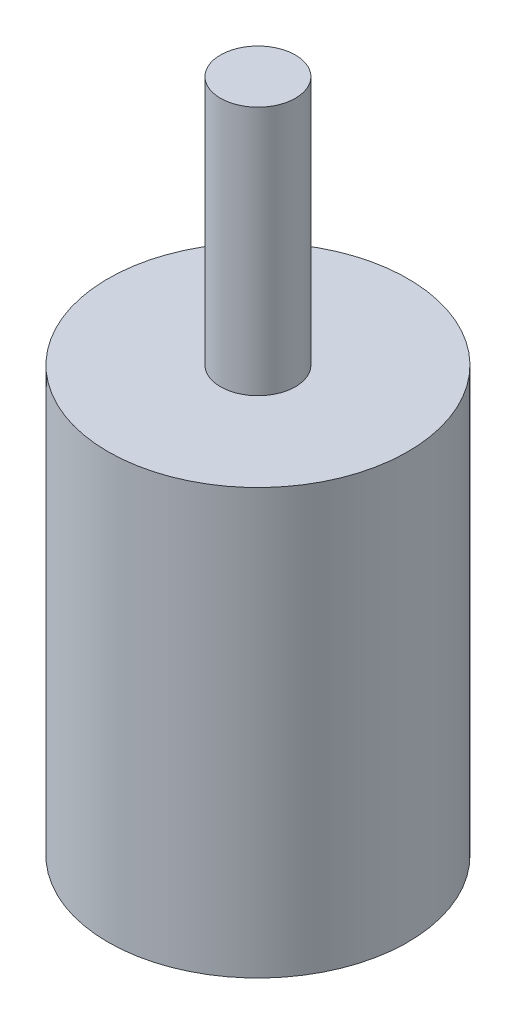
SolidWorks part; units mm, degrees
ref_plane "Front Plane" through (0, 0, 0) normal (0, 0, 1) x (1, 0, 0)
ref_plane "Top Plane" through (0, 0, 0) normal (0, 1, 0) x (1, 0, 0)
ref_plane "Right Plane" through (0, 0, 0) normal (1, 0, 0) x (0, 0, -1)
other "Bounding Box"
ref_plane "Default Plane" through (-8.9266, -12.7485, 0) normal (-0.1736, 0.9848, 0) x (0.9848, 0.1736, 0)
sketch "Sketch1" plane through (0, 0, 0) normal (0, 1, 0) x (1, 0, 0)
  circle A0 centre (0, 0) radius 12
  dimension "D1" = 24
extrude "Boss-Extrude1" add sketch "Sketch1" along normal mid plane 34
sketch "Sketch2" plane through (0, 17, 0) normal (0, 1, 0) x (1, 0, 0)
  circle A0 centre (0, 0) radius 3
  dimension "D1" = 6
extrude "Boss-Extrude2" add sketch "Sketch2" along normal offset from surface (20 mm away) 54 up to face at (0, -17, 12)
